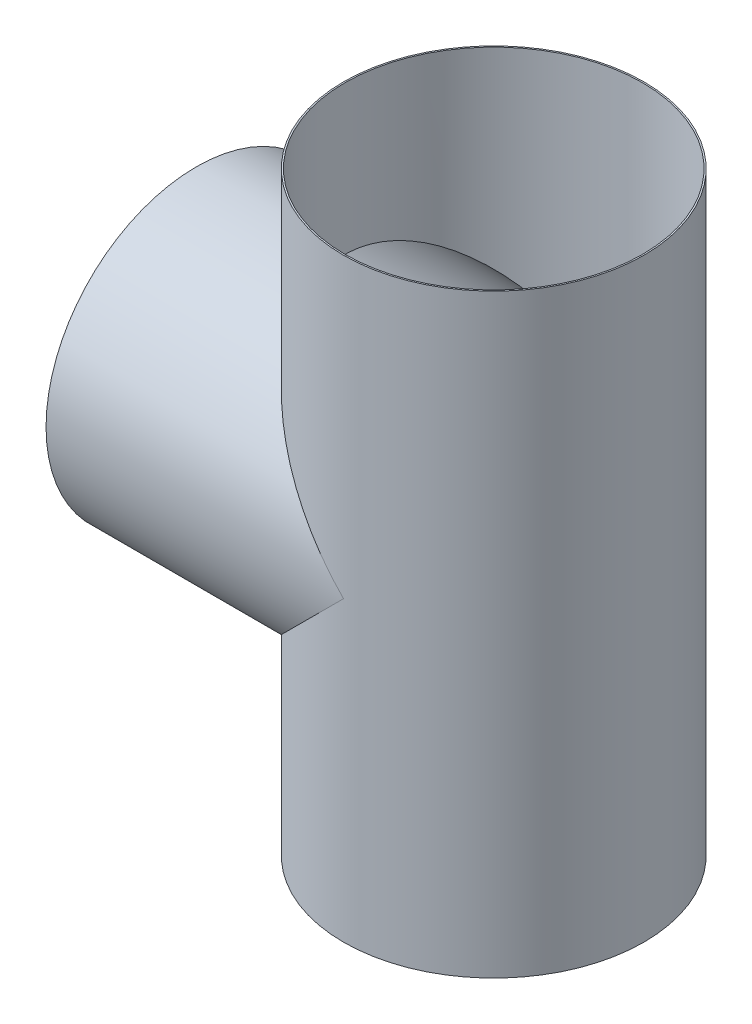
SolidWorks part; units mm, degrees
material "Gray Cast Iron"
ref_plane "Front Plane" through (0, 0, 0) normal (0, 0, 1) x (1, 0, 0)
ref_plane "Top Plane" through (0, 0, 0) normal (0, 1, 0) x (1, 0, 0)
ref_plane "Right Plane" through (0, 0, 0) normal (1, 0, 0) x (0, 0, -1)
sketch "Sketch4" plane through (0, 0, 0) normal (0, 0, 1) x (1, 0, 0)
  line L1 (0, 200) -> (200, 200)
  line L3 (200, 200) -> (200, 400)
  line L4 (200, 200) -> (200, 0)
sketch "Sketch5" plane through (0, 0, 0) normal (0, 1, 0) x (1, 0, 0)
  line L0 (0, 0) -> (200, 0) construction
  circle A1 centre (200, 0) radius 101
sketch "Sketch10" plane through (0, 0, 0) normal (1, 0, 0) x (0, 0, -1)
  line L0 (0, 200) -> (0, 0) construction
  line L1 (0, 200) -> (0, 400) construction
  circle A0 centre (0, 200) radius 101
extrude "Boss-Extrude5" add sketch "Sketch10" along normal blind 200
extrude "Boss-Extrude6" add sketch "Sketch5" along normal blind 400
sketch "Sketch11" plane through (0, 400, 0) normal (0, 1, 0) x (1, 0, 0)
  line L0 (0, 0) -> (200, 0) construction
  circle A0 centre (200, 0) radius 100
extrude "Cut-Extrude1" cut sketch "Sketch11" against normal blind 400
sketch "Sketch12" plane through (0, 0, 0) normal (-1, 0, 0) x (0, 0, 1)
  line L0 (0, 200) -> (0, 0) construction
  line L1 (0, 200) -> (0, 400) construction
  circle A0 centre (0, 200) radius 100
extrude "Cut-Extrude2" cut sketch "Sketch12" against normal blind 200
